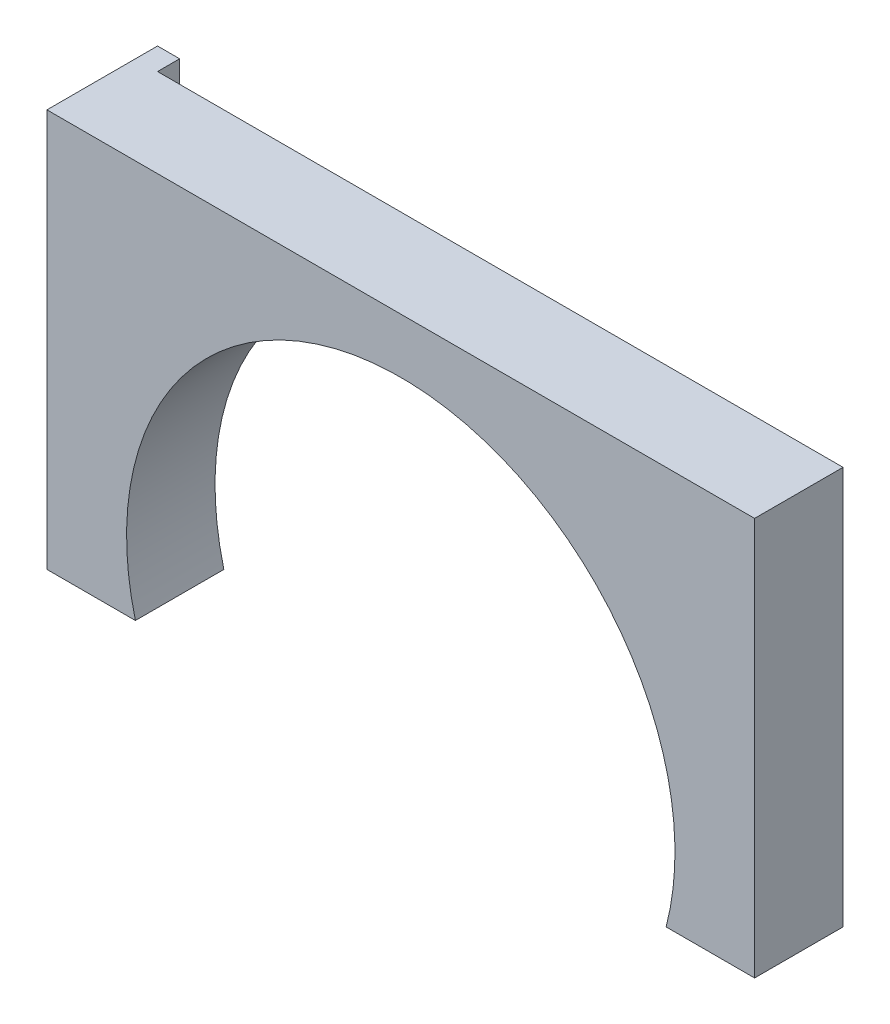
SolidWorks part; units mm, degrees
ref_plane "Front Plane" through (0, 0, 0) normal (0, 0, 1) x (1, 0, 0)
ref_plane "Top Plane" through (0, 0, 0) normal (0, 1, 0) x (1, 0, 0)
ref_plane "Right Plane" through (0, 0, 0) normal (1, 0, 0) x (0, 0, -1)
sketch "Sketch1" plane through (0, 0, 0) normal (0, 0, 1) x (1, 0, 0)
  line L6 (0, 74.3795) -> (0, -15.6205) construction
  line L7 (-80, 74.3795) -> (-80, -15.6205)
  line L10 (80, 74.3795) -> (80, -15.6205)
  line L12 (-60, -15.6205) -> (60, -15.6205) construction
  line L13 (-60, -15.6205) -> (-80, -15.6205)
  line L14 (60, -15.6205) -> (80, -15.6205)
  line L15 (-80, 74.3795) -> (80, 74.3795)
  arc A2 (60, -15.6205) -> (-60, -15.6205) centre (0, 0) ccw
  dimension "D1" = 62
  dimension "D3" = 80
  dimension "D4" = 120
  dimension "D2" = 80
  dimension "D5" = 90
extrude "Boss-Extrude1" add sketch "Sketch1" along normal blind 20
sketch "Sketch4" plane through (0, 0, 0) normal (0, 0, -1) x (-1, 0, 0)
  line L0 (80, -15.6205) -> (60, -15.6205) construction
  line L1 (80, 74.3795) -> (75, 74.3795)
  line L6 (80, 74.3795) -> (80, -15.6205)
  line L7 (80, -15.6205) -> (75, -15.6205)
  line L8 (75, 74.3795) -> (75, -15.6205)
  dimension "D1" = 5
extrude "Boss-Extrude4" add sketch "Sketch4" along normal blind 5
